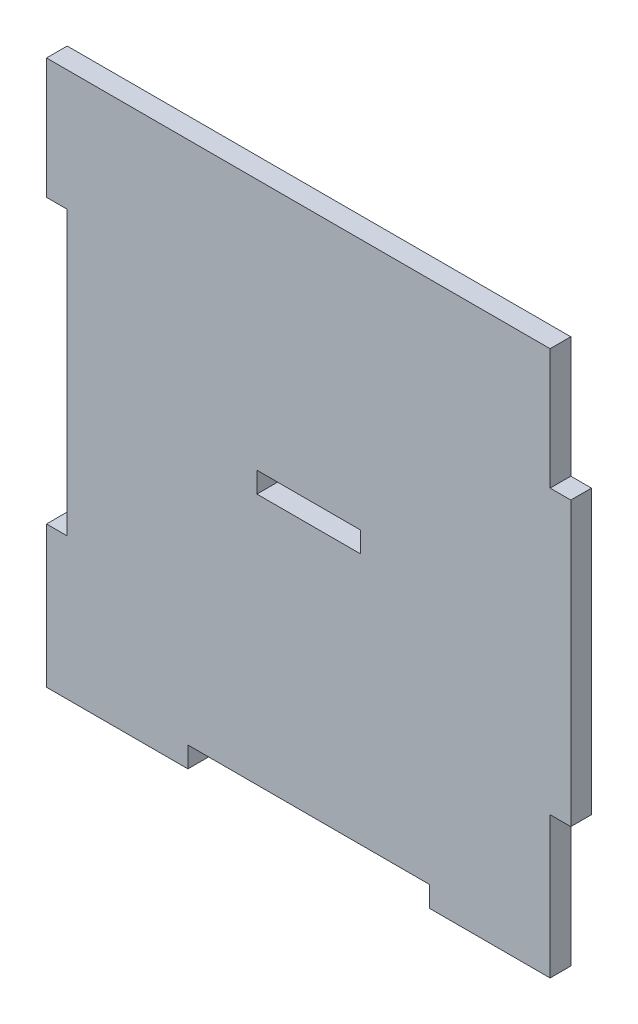
SolidWorks part; units mm, degrees
ref_plane "Front Plane" through (0, 0, 0) normal (0, 0, 1) x (1, 0, 0)
ref_plane "Top Plane" through (0, 0, 0) normal (0, 1, 0) x (1, 0, 0)
ref_plane "Right Plane" through (0, 0, 0) normal (1, 0, 0) x (0, 0, -1)
sketch "Sketch1" plane through (0, 0, 0) normal (0, 0, 1) x (1, 0, 0)
  line L0 (0, 35) -> (0, -38) construction
  line L5 (-35, 38) -> (-17.5, 38)
  line L6 (-35, 20.5) -> (-35, -20.5)
  line L7 (-17.5, -38) -> (17.5, -38)
  line L24 (35, 38) -> (35, 20.5)
  line L25 (-35, 38) -> (35, -38) construction
  line L26 (-35, -38) -> (35, 38) construction
  line L27 (-35, 0) -> (35, 0) construction
  line L31 (-35, -20.5) -> (-38, -20.5)
  line L32 (-35, 20.5) -> (-38, 20.5)
  line L33 (-38, 20.5) -> (-38, 38)
  line L34 (-38, 38) -> (-35, 38)
  line L35 (-38, -20.5) -> (-38, -38)
  line L36 (-17.5, 38) -> (17.5, 38)
  line L37 (35, -38) -> (35, -41)
  line L38 (35, -20.5) -> (38, -20.5)
  line L39 (35, -41) -> (17.5, -41)
  line L40 (35, 20.5) -> (38, 20.5)
  line L41 (17.5, -41) -> (17.5, -38)
  line L42 (-17.5, -38) -> (-17.5, -41)
  line L43 (38, 20.5) -> (38, -20.5)
  line L45 (-35, -41) -> (-17.5, -41)
  line L46 (17.5, 38) -> (35, 38)
  line L47 (35, -20.5) -> (35, -38)
  line L48 (-38, -38) -> (-38, -41)
  line L49 (-38, -41) -> (-35, -41)
  point P0 (0, 0)
  dimension "D1" = 76
  dimension "D2" = 70
  dimension "D3" = 17.5
  dimension "D4" = 17.5
  dimension "D5" = 3
  dimension "D6" = 3
  dimension "D7" = 3
extrude "Boss-Extrude1" add sketch "Sketch1" along normal blind 3
sketch "Sketch2" plane through (0, 0, 3) normal (0, 0, 1) x (1, 0, 0)
  line L0 (-38, -41) -> (-17.5, -41) construction
  line L1 (-7.5, -1.5) -> (7.5, -1.5)
  line L2 (-7.5, -1.5) -> (-7.5, 1.5)
  line L3 (-7.5, 1.5) -> (7.5, 1.5)
  line L4 (7.5, -1.5) -> (7.5, 1.5)
  line L5 (-7.5, -1.5) -> (7.5, 1.5) construction
  line L6 (-7.5, 1.5) -> (7.5, -1.5) construction
  point P0 (0, 0)
  dimension "D1" = 15
  dimension "D2" = 3
extrude "Cut-Extrude1" cut sketch "Sketch2" against normal blind 3
